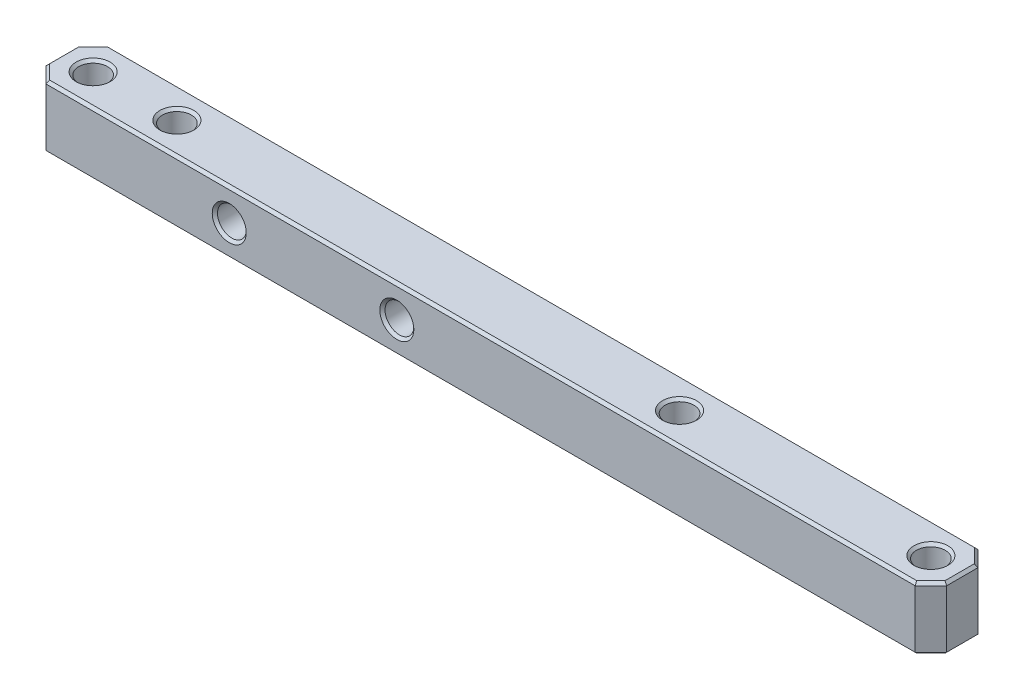
SolidWorks part; units mm, degrees
ref_plane "Front Plane" through (0, 0, 0) normal (0, 0, 1) x (1, 0, 0)
ref_plane "Top Plane" through (0, 0, 0) normal (0, 1, 0) x (1, 0, 0)
ref_plane "Right Plane" through (0, 0, 0) normal (1, 0, 0) x (0, 0, -1)
sketch "Sketch1" plane through (0, 0, 0) normal (0, 1, 0) x (1, 0, 0)
  line L3 (-4.7625, 4.7625) -> (131.7625, 4.7625)
  line L4 (-4.7625, 4.7625) -> (-4.7625, -4.7625)
  line L5 (-4.7625, -4.7625) -> (131.7625, -4.7625)
  line L6 (131.7625, 4.7625) -> (131.7625, -4.7625)
  circle A2 centre (0, 0) radius 2.1828
  circle A3 centre (12.7, 0) radius 2.1828
  circle A4 centre (127, 0) radius 2.1828
  circle A5 centre (88.9, 0) radius 2.1828
  dimension "D2" = 88.9
  dimension "D4" = 4.3656
  dimension "D5" = 4.3656
  dimension "D6" = 4.3656
  dimension "D8" = 4.3656
  dimension "D1" = 12.7
  dimension "D3" = 127
  dimension "D7" = 4.7625
  dimension "D9" = 9.525
  dimension "D10" = 4.7625
  dimension "D11" = 4.7625
extrude "Boss-Extrude1" add sketch "Sketch1" along normal blind 9.525
sketch "Sketch2" plane through (0, 0, 4.7625) normal (0, 0, 1) x (1, 0, 0)
  circle A0 centre (25.4, 4.7625) radius 2.1828
  circle A1 centre (50.8, 4.7625) radius 2.1828
  point P8 (25.0213, 2.6128)
  dimension "D4" = 4.3656
  dimension "D5" = 4.3656
  dimension "D1" = 25.4
  dimension "D2" = 4.7625
  dimension "D3" = 25.4
extrude "Cut-Extrude1" cut sketch "Sketch2" against normal through all both and the other way through all
chamfer "Chamfer1" distance 2.3813 angle 45 4 edges at (131.7625, 4.7625, -4.7625) (131.7625, 4.7625, 4.7625) (-4.7625, 4.7625, -4.7625) (-4.7625, 4.7625, 4.7625)
chamfer "Chamfer2" distance 0.3969 angle 45 28 edges at (23.2172, 4.7625, 4.7625) (27.5828, 4.7625, -4.7625) (48.6172, 4.7625, 4.7625) (52.9828, 4.7625, -4.7625) (88.9, 0, 2.1828) (127, 0, 2.1828) (12.7, 0, 2.1828) (0, 0, 2.1828) (-3.5719, 0, -3.5719) (-4.7625, 0, 0) (-3.5719, 0, 3.5719) (63.5, 0, 4.7625) (130.5719, 0, 3.5719) (131.7625, 0, 0) (130.5719, 0, -3.5719) (63.5, 0, -4.7625) (88.9, 9.525, 2.1828) (12.7, 9.525, 2.1828) (130.5719, 9.525, 3.5719) (63.5, 9.525, 4.7625) (-3.5719, 9.525, 3.5719) (-4.7625, 9.525, 0) (-3.5719, 9.525, -3.5719) (63.5, 9.525, -4.7625) (130.5719, 9.525, -3.5719) (131.7625, 9.525, 0) (0, 9.525, 2.1828) (127, 9.525, 2.1828)
